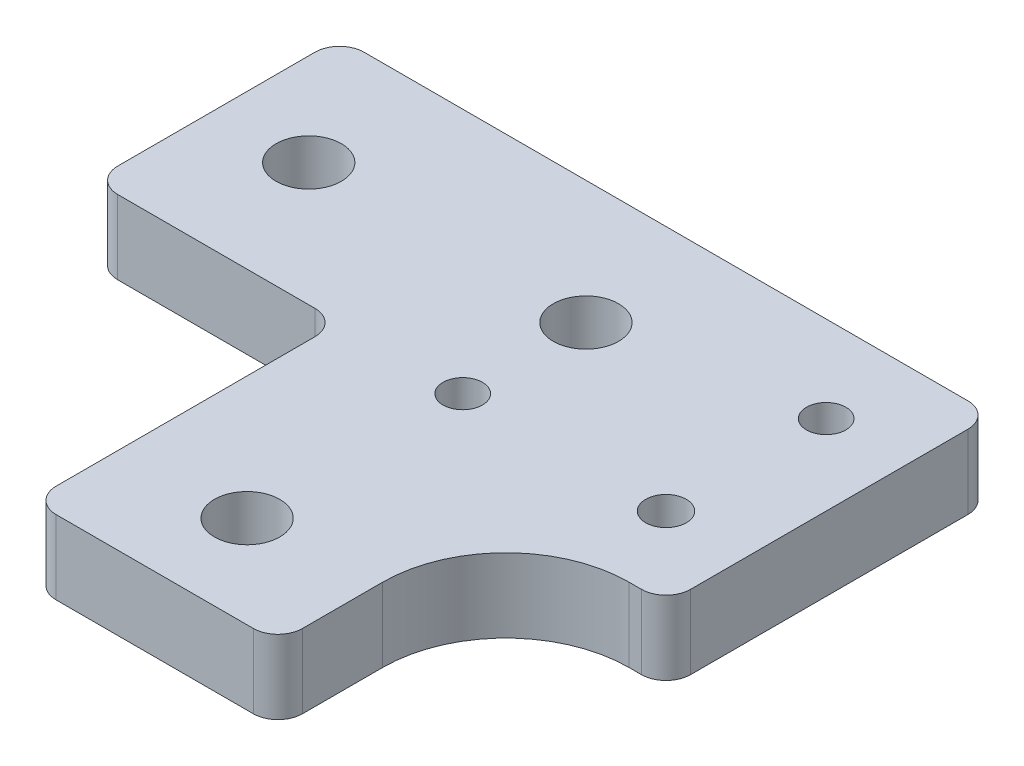
SolidWorks part; units mm, degrees
ref_plane "Front Plane" through (0, 0, 0) normal (0, 0, 1) x (1, 0, 0)
ref_plane "Top Plane" through (0, 0, 0) normal (0, 1, 0) x (1, 0, 0)
ref_plane "Right Plane" through (0, 0, 0) normal (1, 0, 0) x (0, 0, -1)
sketch "Sketch1" plane through (0, 0, 0) normal (0, 1, 0) x (1, 0, 0)
  line L0 (-6.4968, 35.0373) -> (69.4129, 35.0373) construction
  line L2 (20, 0.0373) -> (40, 0.0373) construction
  line L3 (22, 0.0373) -> (38, 0.0373)
  line L4 (0, 27.0373) -> (0, 43.0373)
  line L5 (2, 45.0373) -> (51, 45.0373)
  line L6 (53, 20.5373) -> (53, 43.0373)
  line L9 (2, 25.0373) -> (18, 25.0373)
  line L10 (20, 2.0373) -> (20, 23.0373)
  line L11 (0, 25.0373) -> (0, 45.0373) construction
  line L13 (51, 18.5373) -> (50, 18.5373)
  line L14 (40, 2.0373) -> (40, 8.5373)
  line L15 (30, 49.8846) -> (30, -15.0832) construction
  line L16 (46.5, 48.1369) -> (46.5, 12.2717) construction
  line L17 (23.8975, 25.0373) -> (55.8875, 25.0373) construction
  arc A0 (50, 18.5373) -> (40, 8.5373) centre (50, 8.5373) ccw
  arc A1 (0, 43.0373) -> (2, 45.0373) centre (2, 43.0373) cw
  arc A2 (0, 27.0373) -> (2, 25.0373) centre (2, 27.0373) ccw
  arc A3 (18, 25.0373) -> (20, 23.0373) centre (18, 23.0373) cw
  arc A4 (22, 0.0373) -> (20, 2.0373) centre (22, 2.0373) cw
  arc A5 (38, 0.0373) -> (40, 2.0373) centre (38, 2.0373) ccw
  arc A6 (53, 20.5373) -> (51, 18.5373) centre (51, 20.5373) cw
  arc A7 (51, 45.0373) -> (53, 43.0373) centre (51, 43.0373) cw
  point P13 (30, 35.0373)
  point P14 (7.5, 35.0373)
  point P15 (30, 7.5373)
  point P19 (46.5, 38.0373)
  point P20 (30, 25.0373)
  point P21 (46.5, 25.0373)
  point P22 (23.8975, 25.0373)
  point P33 (20, 25.0373)
  point P44 (53, 45.0373)
  dimension "D15" = 10
  dimension "D16" = 2
  dimension "D1" = 53
  dimension "D2" = 18.5
  dimension "D3" = 20
  dimension "D4" = 25
  dimension "D5" = 20
  dimension "D6" = 26.5
  dimension "D7" = 10
  dimension "D8" = 10
  dimension "D9" = 7.5
  dimension "D10" = 7.5
  dimension "D11" = 6.5
  dimension "D12" = 7
  dimension "D13" = 13
  dimension "D14" = 16.5
extrude "Boss-Extrude1" add sketch "Sketch1" along normal blind 6
hole_wizard "M5 Clearance Hole1" positions "Sketch2" profile "Sketch4" hole size "M5" standard "ANSI Metric" end condition through all
sketch "Sketch2" plane through (0, 0, 0) normal (0, -1, 0) x (-1, 0, 0)
  point P0 (-7.5, 35.0373)
  point P3 (-30, 35.0373)
  point P6 (-30, 7.5373)
sketch "Sketch4" plane through (7.5, 0, -35.0373) normal (1, 0, 0) x (0, 0, -1)
  line L0 (0, 0) -> (0, 6)
  line L1 (0, 6) -> (2.65, 6)
  line L2 (2.65, 6) -> (2.65, 0)
  line L5 (2.65, 0) -> (0, 0)
  line L11 (0, -6.35) -> (0, 107.95) construction
  dimension "Thru Hole Dia." = 5.3
  dimension "Thru Hole Depth" = 6
hole_wizard "M3 Clearance Hole1" positions "Sketch5" profile "Sketch6" hole size "M3" standard "ANSI Metric" end condition through all
sketch "Sketch5" plane through (0, 0, 0) normal (0, -1, 0) x (-1, 0, 0)
  point P0 (-30, 25.0373)
  point P3 (-46.5, 38.0373)
sketch "Sketch6" plane through (30, 0, -25.0373) normal (1, 0, 0) x (0, 0, -1)
  line L0 (0, 0) -> (0, 6)
  line L1 (0, 6) -> (1.6, 6)
  line L2 (1.6, 6) -> (1.6, 0)
  line L5 (1.6, 0) -> (0, 0)
  line L11 (0, -6.35) -> (0, 107.95) construction
  dimension "Thru Hole Dia." = 3.2
  dimension "Thru Hole Depth" = 6
hole_wizard "M4x0.7 Tapped Hole1" positions "Sketch7" profile "Sketch8" tap size "M4x0.7" standard "ANSI Metric" end condition through all
sketch "Sketch7" plane through (0, 0, 0) normal (0, -1, 0) x (-1, 0, 0)
  point P0 (-46.5, 25.0373)
sketch "Sketch8" plane through (46.5, 0, -25.0373) normal (1, 0, 0) x (0, 0, -1)
  line L0 (0, 0) -> (0, 6)
  line L1 (0, 6) -> (1.65, 6)
  line L2 (1.65, 6) -> (1.65, 0)
  line L5 (1.65, 0) -> (0, 0)
  line L11 (0, -6.35) -> (0, 107.95) construction
  dimension "Thru Tap Drill Dia." = 3.3
  dimension "Thru Tap Drill Depth" = 6
cosmetic thread "Hole Thread1" parameters "D2"=4
